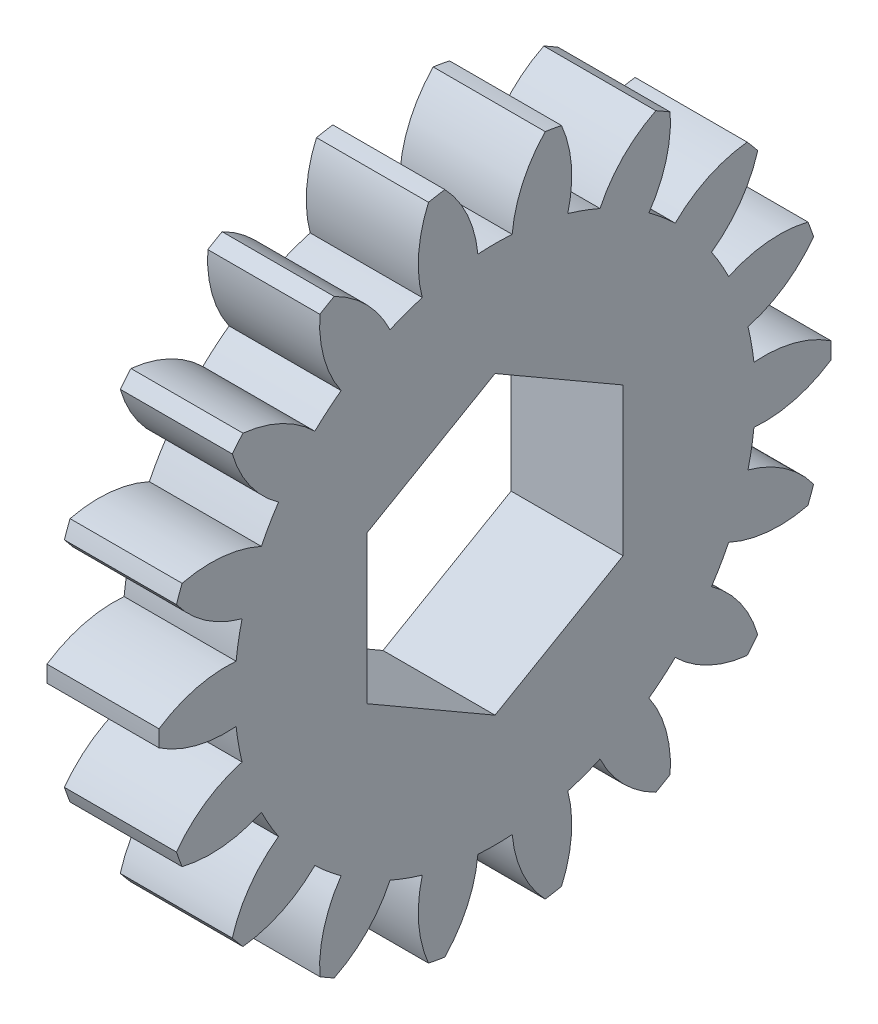
SolidWorks part; units mm, degrees
ref_plane "Plane1" through (0, 0, 0) normal (0, 0, 1) x (1, 0, 0)
ref_plane "Plane2" through (0, 0, 0) normal (0, 1, 0) x (1, 0, 0)
ref_plane "Plane3" through (0, 0, 0) normal (1, 0, 0) x (0, 0, -1)
sketch "HoldingSke" plane through (0, 0, 0) normal (0, 1, 0) x (1, 0, 0)
  line L0 (0, 0) -> (1.0567, -0.3434)
  line L1 (-15, 0) -> (100, 0) construction
  line L2 (0, 0) -> (-2.1039, 2.3779)
  line L3 (0, 0) -> (-11.863, 4.5341)
  line L4 (0, 0) -> (8.2133, 2.6687)
  line L5 (0, 0) -> (-46.8476, -17.4728)
  line L6 (0, 0) -> (-2.4869, -1.6779)
  line L7 (-2.1039, 2.3779) -> (8.6586, 51.2061)
  line L8 (-76.2, 54.61) -> (-75.2, 54.61)
  line L9 (-71.009, 38.7566) -> (-53.1078, 45.2721)
  line L10 (-76.2, 71.12) -> (104.1128, 71.12)
  line L11 (0, 0) -> (-3, 0)
  line L12 (-76.2, 101.6) -> (-76.166, 101.6)
  line L13 (24.9733, 27.94) -> (52.9518, 28.4284)
  line L14 (24.9733, 27.94) -> (24.9743, 27.94)
  line L15 (24.9733, 27.94) -> (100.4006, 29.5858)
  line L16 (-63.627, -0.9) -> (-12.827, -0.9)
  circle A0 centre (0, 0) radius 3
  circle A1 centre (0, 0) radius 6.974
  circle A2 centre (0, 0) radius 37.5
  circle A3 centre (0, 0) radius 3
  dimension "MHD" = 13.948
  dimension "Hub_dia" = 75
  dimension "Bore" = 6
  dimension "MBD" = 6
  dimension "Num_teeth" = 18
  dimension "Pitch" = 1.1111
  dimension "Overall_len" = 50
  dimension "Show_teeth" = 18
  dimension "Thickness" = 3
  dimension "OAL" = 50.0003
  dimension "T_dim" = 1
  dimension "Ap" = 20
  dimension "H" = 19.05
  dimension "Pitch_radius" = 180.3128
  dimension "Width" = 3
  dimension "Backlash" = 0.034
  dimension "Addendum_fac" = 1
  dimension "Dedendum_fac" = 1.25
  dimension "Clearance_fac" = 0.25
  dimension "Dedendum_add" = 0.001
  dimension "Module" = 0.9
sketch "BasProSke" plane through (0, 0, 0) normal (0, 1, 0) x (1, 0, 0)
  line L0 (-10, 0) -> (60, 0) construction
  line L1 (0, 0) -> (0, 9)
  line L2 (0, 0) -> (3, 0)
  line L3 (3, 0) -> (3, 9)
  line L4 (3, 9) -> (0, 9)
  dimension "Thickness" = 3
  dimension "Diameter" = 18
revolve "Base-Revolve" add sketch "BasProSke" angle 360 about L0
sketch "TooCutSke" plane through (0, 0, 0) normal (1, 0, 0) x (0, 0, -1)
  line L1 (0, 0) -> (0, 107) construction
  line L2 (0, 0) -> (-0.7654, 8.0638) construction
  line L3 (0, 0) -> (-2.8041, 15.903) construction
  line L4 (-0.7654, 8.0638) -> (-1.4021, 7.9515) construction
  arc A0 (0.4593, 6.9589) -> (-0.4593, 6.9589) centre (0, 0) ccw
  arc A1 (1.3655, 8.9215) -> (-1.3655, 8.9215) centre (0, 0) ccw
  circle A2 centre (0, 0) radius 8.1 construction
  circle A3 centre (0, 0) radius 7.6115 construction
  arc A4 (-0.4593, 6.9589) -> (-1.3655, 8.9215) centre (-3.6854, 6.6598) ccw
  arc A5 (1.3655, 8.9215) -> (0.4593, 6.9589) centre (3.6854, 6.6598) ccw
  dimension "Root_dia" = 13.948
  dimension "Overcut_dia" = 18.0508
  dimension "Pitch_dia" = 16.2
  dimension "Base_dia" = 15.223
  dimension "Flank_rad" = 3.24
  dimension "Half_ang" = 10
  dimension "Half_CT" = 0.6465
extrude "ToothCut" cut sketch "TooCutSke" along normal through all
fillet "Breaks" [suppressed] radius 0.018
fillet "RootFillets" [suppressed] radius 0.226
pattern_circular "TeethCuts" count 18 every 20 about axis through (-10, 0, 0) along (1, 0, 0) of "ToothCut", "RootFillets", "Breaks"
sketch "HubNeaOneSke" plane through (0, 0, 0) normal (-1, 0, 0) x (0, 0, 1)
  circle A0 centre (0, 0) radius 6.974
  dimension "Diameter" = 13.948
extrude "HubNearOne" [suppressed] add sketch "HubNeaOneSke" along normal blind 47.0003
sketch "HubNeaBotSke" plane through (0, 0, 0) normal (-1, 0, 0) x (0, 0, 1)
  circle A0 centre (0, 0) radius 6.974
  dimension "Diameter" = 13.948
extrude "HubNearBoth" [suppressed] add sketch "HubNeaBotSke" along normal blind 23.5001
ref_plane "FarPln" through (3, 0, 0) normal (1, 0, 0) x (0, 0, -1)
sketch "HubFarSke" plane through (3, 0, 0) normal (1, 0, 0) x (0, 0, -1)
  circle A0 centre (0, 0) radius 6.974
  dimension "Diameter" = 13.948
extrude "HubFar" [suppressed] add sketch "HubFarSke" along normal blind 23.5001
sketch "KeySke" plane through (0, 0, 0) normal (1, 0, 0) x (0, 0, -1)
  line L0 (-1, 0) -> (-1, 4)
  line L1 (-1, 4) -> (1, 4)
  line L2 (1, 4) -> (1, 0)
  line L3 (0, 0) -> (0, 34) construction
  line L4 (-1, 0) -> (1, 0)
  dimension "Offset" = 4
  dimension "Width" = 2
extrude "Keyway" [suppressed] cut sketch "KeySke" along normal mid plane 100.0005
pattern_circular "Keyway2" [suppressed] count 2 every 90 about axis through (-10, 0, 0) along (1, 0, 0)
sketch "Sketch1" plane through (3, 0, 0) normal (1, 0, 0) x (0, 0, -1)
  line L1 (0, 3.9606) -> (-3.43, 1.9803)
  line L2 (-3.43, 1.9803) -> (-3.43, -1.9803)
  line L3 (-3.43, -1.9803) -> (0, -3.9606)
  line L4 (0, -3.9606) -> (3.43, -1.9803)
  line L5 (3.43, -1.9803) -> (3.43, 1.9803)
  line L6 (3.43, 1.9803) -> (0, 3.9606)
  circle A1 centre (0, 0) radius 3.43 construction
  dimension "D1" = 6.86
extrude "Cut-Extrude1" cut sketch "Sketch1" against normal through all
equation "' \"Module@HoldingSke\" = 6.35"
equation "' \"Num_teeth@HoldingSke\" = 12"
equation "' \"Ap@HoldingSke\" =  20"
equation "' \"Ap@HoldingSke\" = 20"
equation "' \"Width@HoldingSke\" = 0.5 * 25.4"
equation "' \"Hub_dia@HoldingSke\"= 1 * 25.4"
equation "' \"Hub_dia@HoldingSke\" = 1 * 25.4"
equation "' \"Overall_len@HoldingSke\" = 1.0 * 25.4"
equation "' \"Bore@HoldingSke\" = 0.75 * 25.4"
equation "' \"T_dim@HoldingSke\" = 0.1 * 25.4"
equation "' \"Width@KeySke\" = 0.25 * 25.4"
equation "' \"Show_teeth@HoldingSke\" = 13"
equation "' \"Backlash@HoldingSke\" = 0.009 * 25.4"
equation "' \"Addendum_fac@HoldingSke\" = 1.0"
equation "' \"Dedendum_fac@HoldingSke\" = 1.25"
equation "' \"Dedendum_add@HoldingSke\" = 0.00005 * 25.4"
equation "' \"Clearance_fac@HoldingSke\" = 0.25"
equation "\"Pitch@HoldingSke\" = 1 / \"Module@HoldingSke\""
equation "\"Overcut_dia@TooCutSke\" = (\"Num_teeth@HoldingSke\" + 2 * \"Addendum_fac@HoldingSke\") / \"Pitch@HoldingSke\" + 0.002 * 25.4"
equation "\"Pitch_dia@TooCutSke\" = \"Num_teeth@HoldingSke\" / \"Pitch@HoldingSke\""
equation "\"Base_dia@TooCutSke\" = \"Num_teeth@HoldingSke\" / \"Pitch@HoldingSke\" * cos((\"Ap@HoldingSke\"  * 3.14159265 / 180))"
equation "\"Root_dia@TooCutSke\" = (\"Num_teeth@HoldingSke\" + 2) / \"Pitch@HoldingSke\" - 2 * (\"Addendum_fac@HoldingSke\" + \"Dedendum_fac@HoldingSke\") / \"Pitch@HoldingSke\" - \"Dedendum_add@HoldingSke\" * 2"
equation "\"Half_ang@TooCutSke\" = 180 / \"Num_teeth@HoldingSke\""
equation "\"Half_CT@TooCutSke\" = \"Num_teeth@HoldingSke\" / \"Pitch@HoldingSke\" * sin((3.14159265 / 2 / \"Num_teeth@HoldingSke\")) / 2 - 7 * \"Backlash@HoldingSke\" / 4"
equation "\"Flank_rad@TooCutSke\" = \"Num_teeth@HoldingSke\" / \"Pitch@HoldingSke\" / 5"
equation "\"Radius@RootFillets\" = \"Clearance_fac@HoldingSke\" / \"Pitch@HoldingSke\" + \"Dedendum_add@HoldingSke\""
equation "\"Break_rad@Breaks\" = 0.02 / \"Pitch@HoldingSke\""
equation "\"Thickness@HoldingSke\" = \"Width@HoldingSke\""
equation "\"OAL@HoldingSke\" = \"Thickness@HoldingSke\""
equation "\"MHD@HoldingSke\" = (\"Num_teeth@HoldingSke\" + 2) / \"Pitch@HoldingSke\" - 2 * (\"Addendum_fac@HoldingSke\" + \"Dedendum_fac@HoldingSke\")  / \"Pitch@HoldingSke\" - \"Dedendum_add@HoldingSke\" * 2"
equation "\"MBD@HoldingSke\" = (\"Num_teeth@HoldingSke\" + 2) / \"Pitch@HoldingSke\" - 2 * (\"Addendum_fac@HoldingSke\" + \"Dedendum_fac@HoldingSke\")  / \"Pitch@HoldingSke\" - \"Dedendum_add@HoldingSke\" * 2 - 0.002 * 25.4"
equation "\"MHD@HoldingSke\" = ((sgn( \"MHD@HoldingSke\" - \"Hub_dia@HoldingSke\" )-1)*( \"MHD@HoldingSke\" - \"Hub_dia@HoldingSke\" ))/-2+ \"Hub_dia@HoldingSke\""
equation "\"MBD@HoldingSke\" = ((sgn( \"MBD@HoldingSke\" - \"Bore@HoldingSke\" )-1)*( \"MBD@HoldingSke\" - \"Bore@HoldingSke\" ))/-2+ \"Bore@HoldingSke\""
equation "\"OAL@HoldingSke\" = ((sgn( \"OAL@HoldingSke\" - \"Overall_len@HoldingSke\" )+1)*( \"OAL@HoldingSke\" - \"Overall_len@HoldingSke\" ))/2 + \"Overall_len@HoldingSke\" + 0.000002 * 25.4"
equation "\"Num_teeth@TeethCuts\" = int( \"Show_teeth@HoldingSke\" ) + 1"
equation "\"Num_teeth@TeethCuts\" = ((sgn( \"Num_teeth@TeethCuts\" - \"Num_teeth@HoldingSke\" )-1)*( \"Num_teeth@TeethCuts\" - \"Num_teeth@HoldingSke\" ))/-2+ \"Num_teeth@HoldingSke\""
equation "\"Num_teeth@TeethCuts\" = ((sgn( \"Num_teeth@TeethCuts\" - 2.0)+1)*( \"Num_teeth@TeethCuts\" - 2.0))/2 +2.0"
equation "\"Angle@TeethCuts\" = 360.0 / \"Num_teeth@HoldingSke\""
equation "\"Diameter@BasProSke\" = (\"Num_teeth@HoldingSke\" + 2 * \"Addendum_fac@HoldingSke\") / \"Pitch@HoldingSke\""
equation "\"Thickness@BasProSke\"  = \"Thickness@HoldingSke\""
equation "' \"Fillet_rad@BasProSke\" =  \"Thickness@HoldingSke\" * 0.05"
equation "' \"Fillet_rad@BasProSke\" = \"Thickness@HoldingSke\" * 0.05"
equation "\"MHD@HoldingSke\" = ((sgn( \"MHD@HoldingSke\" - \"Root_dia@TooCutSke\" )-1)*( \"MHD@HoldingSke\" - \"Root_dia@TooCutSke\" ))/-2+ \"Root_dia@TooCutSke\""
equation "\"Diameter@HubNeaOneSke\" = \"MHD@HoldingSke\""
equation "\"Length@HubNearOne\" = \"OAL@HoldingSke\" - \"Thickness@BasProSke\""
equation "\"Diameter@HubNeaBotSke\" = \"MHD@HoldingSke\""
equation "\"Length@HubNearBoth\" = ( \"OAL@HoldingSke\" - \"Thickness@BasProSke\" ) / 2.0"
equation "\"Thickness@FarPln\" = \"Thickness@BasProSke\""
equation "\"Diameter@HubFarSke\" = \"MHD@HoldingSke\""
equation "\"Length@HubFar\" = ( \"OAL@HoldingSke\" - \"Thickness@BasProSke\" ) / 2.0"
equation "\"D1@Keyway\" = \"OAL@HoldingSke\" * 2.0"
equation "\"Offset@KeySke\" = \"T_dim@HoldingSke\" + \"MBD@HoldingSke\" / 2.0"
